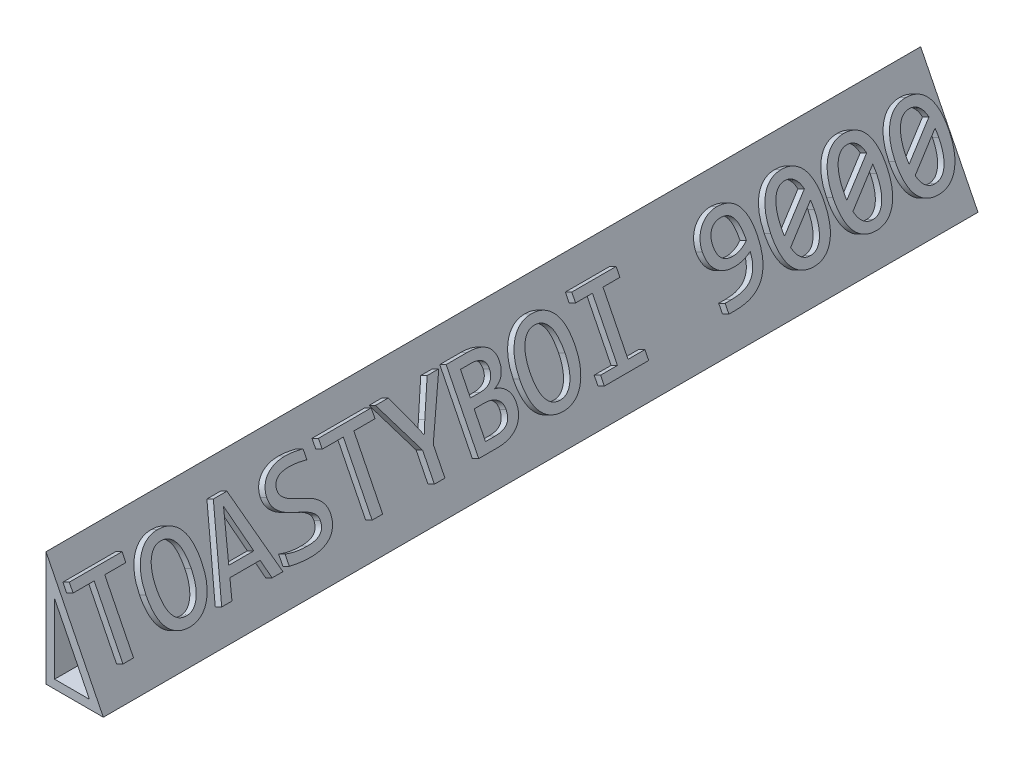
SolidWorks part; units mm, degrees
ref_plane "Front Plane" through (0, 0, 0) normal (0, 0, 1) x (1, 0, 0)
ref_plane "Top Plane" through (0, 0, 0) normal (0, 1, 0) x (1, 0, 0)
ref_plane "Right Plane" through (0, 0, 0) normal (1, 0, 0) x (0, 0, -1)
sketch "Sketch3" plane through (0, 0, 0) normal (0, 0, 1) x (1, 0, 0)
  line L0 (0, 0) -> (20, 0)
  line L1 (20, 0) -> (0, 40)
  line L2 (0, 40) -> (0, 0)
  dimension "D1" = 40
  dimension "D2" = 20
extrude "Boss-Extrude2" add sketch "Sketch3" along normal blind 305
shell "Shell2" thickness 3
sketch "Sketch4" plane through (0, 0, 305) normal (0, 0, 1) x (1, 0, 0)
  line L0 (3, 27.2918) -> (15.1459, 3)
  line L1 (15.1459, 3) -> (3, 3)
  line L2 (3, 3) -> (3, 27.2918)
extrude "Cut-Extrude1" cut sketch "Sketch4" against normal through all both and the other way through all
sketch "Sketch5" plane through (16, 8, 0) normal (0.8944, 0.4472, 0) x (0, 0, -1)
  line L0 (-305, 1.3296) -> (0, 1.3296) construction
  line L1 (-305, -8.9443) -> (-305, 35.7771) construction
  line L2 (0, -8.9443) -> (0, 35.7771) construction
  text T0 "TOASTYBOI 9000" font "Consolas" height 25.4
  point P7 (0, 0)
extrude "Boss-Extrude3" add sketch "Sketch5" along normal blind 2.5
